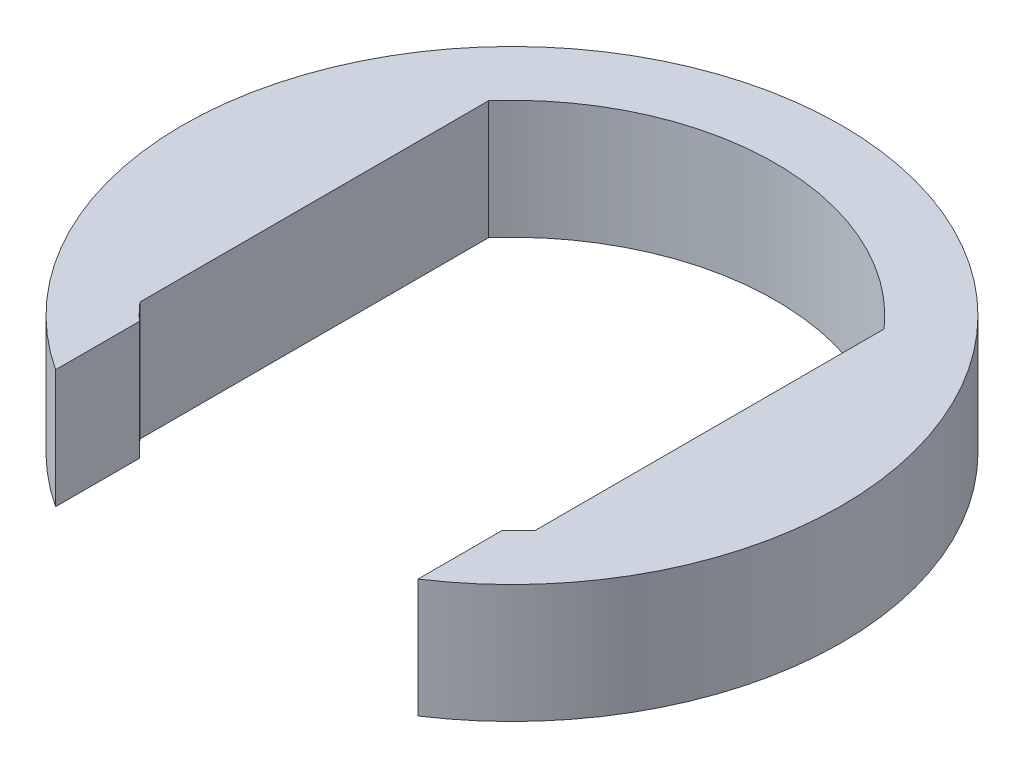
SolidWorks part; units mm, degrees
ref_plane "Front Plane" through (0, 0, 0) normal (0, 0, 1) x (1, 0, 0)
ref_plane "Top Plane" through (0, 0, 0) normal (0, 1, 0) x (1, 0, 0)
ref_plane "Right Plane" through (0, 0, 0) normal (1, 0, 0) x (0, 0, -1)
sketch "Sketch1" plane through (0, 0, 0) normal (0, 1, 0) x (1, 0, 0)
  circle A0 centre (0, 0) radius 5
  dimension "D1" = 10
extrude "Boss-Extrude1" add sketch "Sketch1" along normal blind 1.8
sketch "Sketch2" plane through (0, 1.8, 0) normal (0, 1, 0) x (1, 0, 0)
  line L0 (-3, 2.6458) -> (-3, -2.6458)
  line L1 (3, 2.6458) -> (3, -2.6458)
  line L2 (-2.75, -2.9047) -> (-2.75, -4.1758)
  line L3 (2.75, -2.9047) -> (2.75, -4.1758)
  arc A1 (-3, 2.6458) -> (3, 2.6458) centre (0, 0) cw
  arc A2 (-3, -2.6458) -> (-2.75, -2.9047) centre (0, 0) ccw
  arc A3 (3, -2.6458) -> (2.75, -2.9047) centre (0, 0) cw
  circle A4 centre (0, 0) radius 5 construction
  arc A5 (-2.75, -4.1758) -> (2.75, -4.1758) centre (0, 0) ccw
  point P11 (3, 0)
  dimension "D1" = 4
  dimension "D2" = 0.25
  dimension "D3" = 6
extrude "Cut-Extrude1" cut sketch "Sketch2" against normal through all
